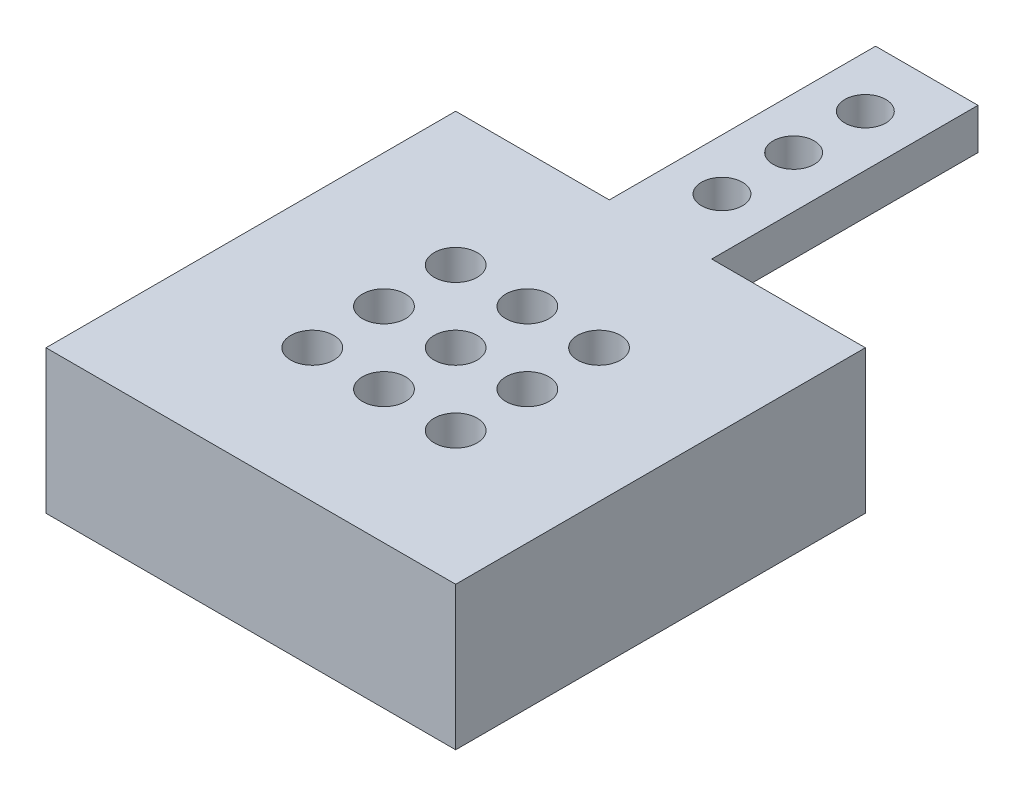
SolidWorks part; units mm, degrees
ref_plane "Front Plane" through (0, 0, 0) normal (0, 0, 1) x (1, 0, 0)
ref_plane "Top Plane" through (0, 0, 0) normal (0, 1, 0) x (1, 0, 0)
ref_plane "Right Plane" through (0, 0, 0) normal (1, 0, 0) x (0, 0, -1)
sketch "Sketch1" plane through (0, 0, 0) normal (0, 1, 0) x (1, 0, 0)
  line L1 (0, 0) -> (40, 0)
  line L2 (0, 0) -> (0, 40)
  line L3 (0, 40) -> (40, 40)
  line L4 (40, 0) -> (40, 40)
  dimension "D1" = 40
  dimension "D2" = 40
extrude "Boss-Extrude1" add sketch "Sketch1" along normal blind 14
sketch "Sketch4" plane through (0, 0, -40) normal (0, 0, -1) x (-1, 0, 0)
  line L1 (-20, 0) -> (-20, 14) construction
  line L2 (-40, 0) -> (0, 0) construction
  line L3 (-40, 14) -> (0, 14) construction
  line L5 (-15, 14) -> (-25, 14)
  line L6 (-15, 14) -> (-15, 10)
  line L7 (-15, 10) -> (-25, 10)
  line L8 (-25, 14) -> (-25, 10)
  point P10 (-20, 10)
  dimension "D1" = 4
  dimension "D2" = 10
extrude "Boss-Extrude3" add sketch "Sketch4" along normal blind 26
sketch "Sketch5" plane through (0, 14, 0) normal (0, 1, 0) x (1, 0, 0)
  line L0 (20, 66) -> (20, 0) construction
  line L1 (15, 66) -> (25, 66) construction
  line L2 (0, 0) -> (40, 0) construction
  circle A0 centre (20, 60) radius 2
  circle A1 centre (20, 53) radius 2
  circle A2 centre (20, 46) radius 2
  dimension "D2" = 4
  dimension "D3" = 4
  dimension "D4" = 4
  dimension "D1" = 6
  dimension "D5" = 7
  dimension "D6" = 7
extrude "Cut-Extrude2" cut sketch "Sketch5" against normal blind 26
sketch "Sketch6" plane through (0, 0, 0) normal (0, -1, 0) x (1, 0, 0)
  line L0 (20, -40) -> (20, 0) construction
  line L1 (40, -40) -> (0, -40) construction
  line L2 (0, 0) -> (40, 0) construction
  line L3 (0, -20) -> (40, -20) construction
  line L4 (0, -40) -> (0, 0) construction
  line L5 (40, 0) -> (40, -40) construction
  circle A0 centre (13, -27) radius 2.1
  circle A1 centre (20, -27) radius 2.1
  circle A2 centre (27, -27) radius 2.1
  circle A3 centre (20, -20) radius 2.1
  circle A4 centre (27, -20) radius 2.1
  circle A5 centre (20, -13) radius 2.1
  circle A6 centre (27, -13) radius 2.1
  circle A7 centre (13, -20) radius 2.1
  circle A8 centre (13, -13) radius 2.1
  dimension "D1" = 4.2
  dimension "D2" = 3
  dimension "D3" = 3
  dimension "D4" = 7
  dimension "D5" = 7
extrude "Cut-Extrude3" cut sketch "Sketch6" against normal through all
